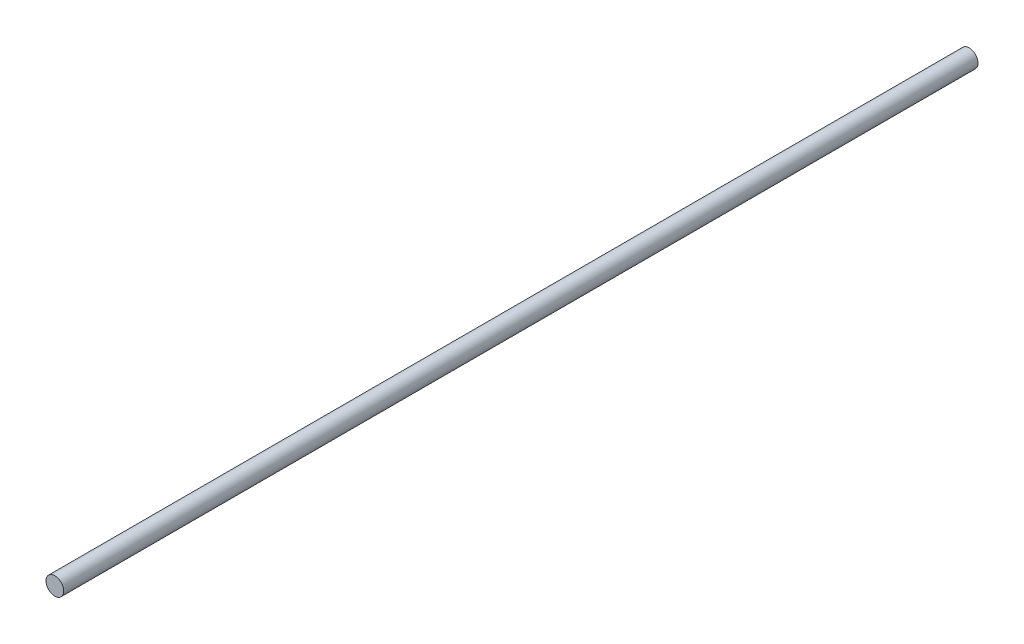
SolidWorks part; units mm, degrees
ref_plane "Front Plane" through (0, 0, 0) normal (0, 0, 1) x (1, 0, 0)
ref_plane "Top Plane" through (0, 0, 0) normal (0, 1, 0) x (1, 0, 0)
ref_plane "Right Plane" through (0, 0, 0) normal (1, 0, 0) x (0, 0, -1)
sketch "Sketch1" plane through (0, 0, 0) normal (0, 0, 1) x (1, 0, 0)
  circle A0 centre (0, 0) radius 15
  dimension "D1" = 30
extrude "Boss-Extrude1" add sketch "Sketch1" along normal blind 1550
